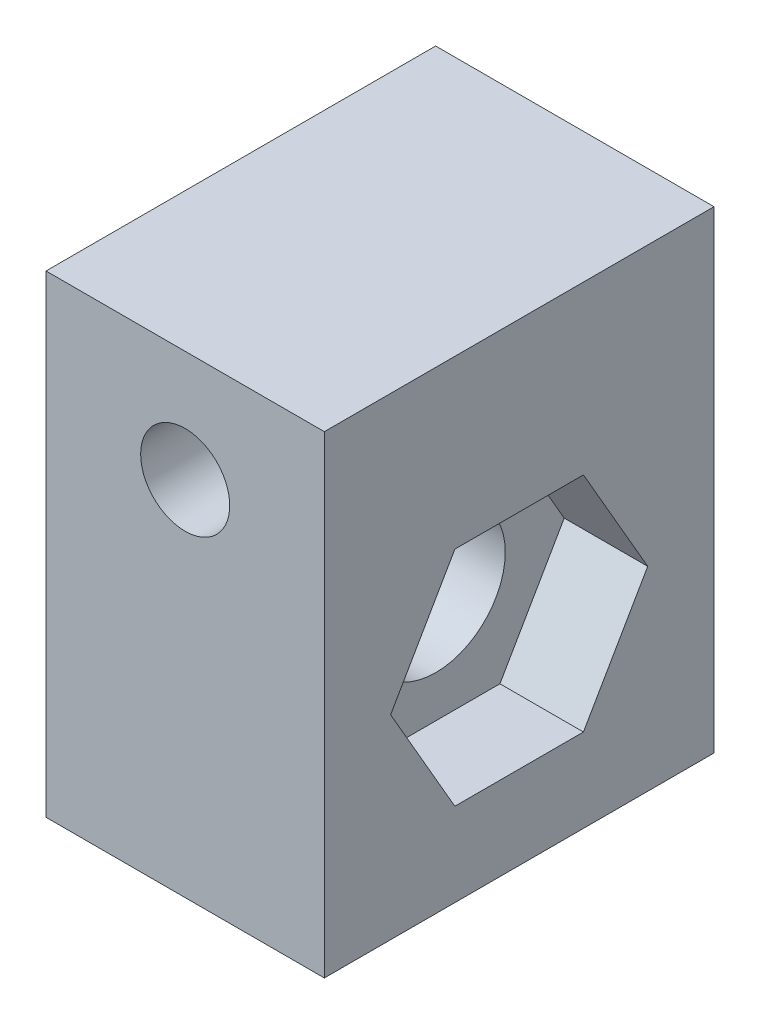
SolidWorks part; units mm, degrees
ref_plane "Front Plane" through (0, 0, 0) normal (0, 0, 1) x (1, 0, 0)
ref_plane "Top Plane" through (0, 0, 0) normal (0, 1, 0) x (1, 0, 0)
ref_plane "Right Plane" through (0, 0, 0) normal (1, 0, 0) x (0, 0, -1)
sketch "Sketch1" plane through (0, 0, 0) normal (0, 0, 1) x (1, 0, 0)
  line L1 (5, -8.5) -> (-5, -8.5)
  line L2 (5, -8.5) -> (5, 8.5)
  line L3 (5, 8.5) -> (-5, 8.5)
  line L4 (-5, -8.5) -> (-5, 8.5)
  line L5 (5, -8.5) -> (-5, 8.5) construction
  line L6 (5, 8.5) -> (-5, -8.5) construction
  point P0 (0, 0)
  dimension "D1" = 17
  dimension "D2" = 10
extrude "Boss-Extrude1" add sketch "Sketch1" along normal blind 14
sketch "Sketch2" plane through (0, 0, 0) normal (0, 0, -1) x (-1, 0, 0)
  line L0 (-5, 8.5) -> (5, 8.5) construction
  line L1 (-5, -8.5) -> (-5, 8.5) construction
  circle A0 centre (0, 4.5) radius 1.6
  dimension "D1" = 3.2
  dimension "D2" = 4
  dimension "D3" = 5
extrude "Cut-Extrude1" cut sketch "Sketch2" against normal through all
sketch "Sketch3" plane through (-5, 0, 0) normal (-1, 0, 0) x (0, 0, 1)
  line L0 (14, 8.5) -> (0, 8.5) construction
  line L1 (2.3812, -1.5) -> (4.6906, -5.5)
  line L2 (4.6906, -5.5) -> (9.3094, -5.5)
  line L3 (9.3094, -5.5) -> (11.6188, -1.5)
  line L4 (11.6188, -1.5) -> (9.3094, 2.5)
  line L5 (9.3094, 2.5) -> (4.6906, 2.5)
  line L6 (4.6906, 2.5) -> (2.3812, -1.5)
  line L7 (14, -8.5) -> (0, -8.5) construction
  circle A0 centre (7, -1.5) radius 4 construction
  point P10 (7, 8.5)
  dimension "D1" = 8
  dimension "D2" = 10
  dimension "D3" = 7
extrude "Cut-Extrude2" cut sketch "Sketch3" against normal blind 3
sketch "Sketch5" plane through (-2, 0, 0) normal (-1, 0, 0) x (0, 0, 1)
  circle A0 centre (7, -1.5) radius 2.5
  dimension "D1" = 5
extrude "Cut-Extrude3" cut sketch "Sketch5" against normal through all
mirror "Mirror1" about plane through (0, 0, 0) normal (1, 0, 0) of "Cut-Extrude2"
